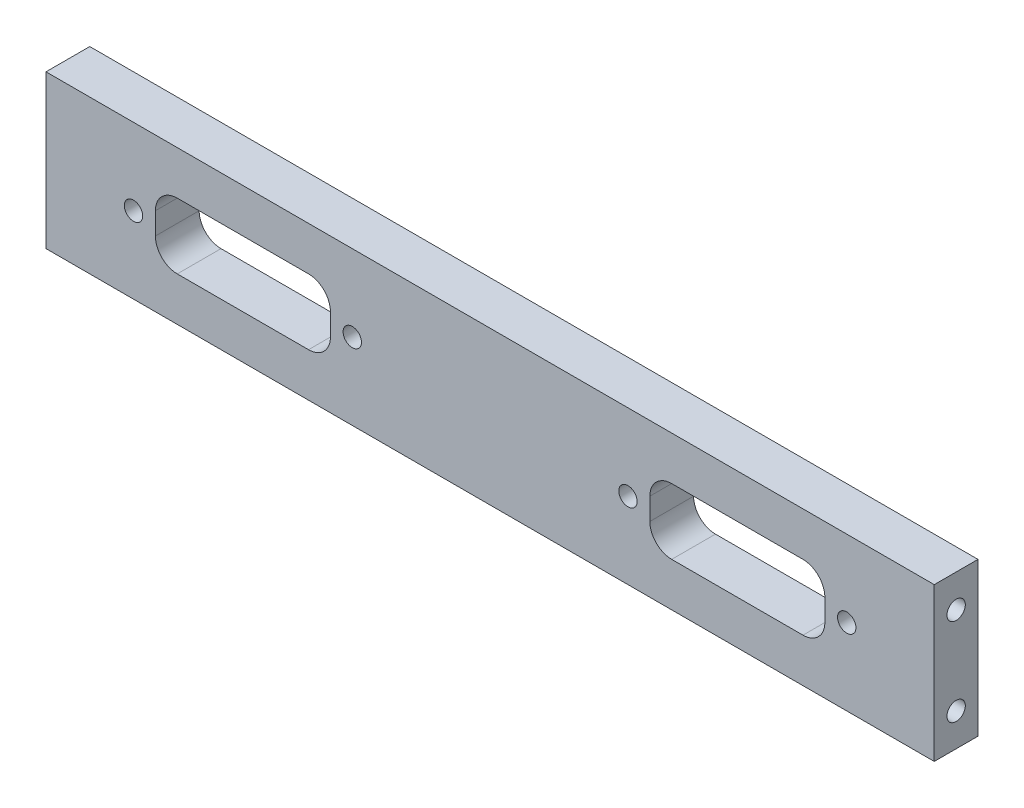
SolidWorks part; units mm, degrees
material "普通碳钢"
ref_plane "前视基准面" through (0, 0, 0) normal (0, 0, 1) x (1, 0, 0)
ref_plane "上视基准面" through (0, 0, 0) normal (0, 1, 0) x (1, 0, 0)
ref_plane "右视基准面" through (0, 0, 0) normal (1, 0, 0) x (0, 0, -1)
sketch "草图1" plane through (0, 0, 0) normal (0, 0, 1) x (1, 0, 0)
  line L1 (-101.5, -17.5) -> (101.5, -17.5)
  line L2 (-101.5, -17.5) -> (-101.5, 17.5)
  line L3 (-101.5, 17.5) -> (101.5, 17.5)
  line L4 (101.5, -17.5) -> (101.5, 17.5)
  line L5 (-101.5, -17.5) -> (101.5, 17.5) construction
  line L6 (-101.5, 17.5) -> (101.5, -17.5) construction
  point P0 (0, 0)
  dimension "D1" = 35
  dimension "D2" = 203
extrude "凸台-拉伸1" add sketch "草图1" along normal mid plane 10 contours L3 L4 L1 L2
hole_wizard "M5 螺纹孔1" positions "草图3" profile "草图2" tap size "M5" standard "GB"
sketch "草图3" plane through (-101.5, 0, 0) normal (-1, 0, 0) x (0, 0, 1)
  point P0 (0, 10)
  point P2 (0, -10)
  dimension "D1" = 20
  dimension "D2" = 10
sketch "草图2" plane through (-101.5, 10, 0) normal (0, 1, 0) x (0, 0, 1)
  line L0 (0, 0) -> (0, 15.2618)
  line L1 (0, 15.2618) -> (2.1, 14)
  line L2 (2.1, 14) -> (2.1, 0)
  line L5 (2.1, 0) -> (0, 0)
  line L10 (0, 15.2618) -> (-2.1, 14) construction
  line L11 (0, -6.35) -> (0, 107.95) construction
  dimension "螺纹孔钻头直径" = 4.2
  dimension "螺纹孔钻头深度" = 14
  dimension "导头角度" = 118
cosmetic thread "孔螺蚊线1" parameters "D1"=10, "D2"=5
cosmetic thread "孔螺蚊线2" parameters "D1"=10, "D2"=5
mirror "镜向1" about plane through (0, 0, 0) normal (1, 0, 0) of "M5 螺纹孔1"
sketch "草图4" plane through (0, 0, -5) normal (0, 0, -1) x (-1, 0, 0)
  line L0 (101.5, -17.5) -> (101.5, 17.5) construction
  line L1 (36.5, -7.5) -> (76.5, -7.5)
  line L2 (36.5, -7.5) -> (36.5, 7.5)
  line L3 (36.5, 7.5) -> (76.5, 7.5)
  line L4 (76.5, -7.5) -> (76.5, 7.5)
  line L5 (36.5, -7.5) -> (76.5, 7.5) construction
  line L6 (36.5, 7.5) -> (76.5, -7.5) construction
  point P0 (56.5, 0)
  dimension "D1" = 40
  dimension "D2" = 15
  dimension "D3" = 25
extrude "切除-拉伸1" cut sketch "草图4" against normal blind 10
fillet "圆角1" radius 5 4 edges at (-76.5, -7.5, 0) (-76.5, 7.5, 0) (-36.5, -7.5, 0) (-36.5, 7.5, 0)
hole_wizard "Ø4.2 (4.2) 直径孔1" positions "草图6" profile "草图5" hole size "Ø4.2" standard "GB" end condition through all
sketch "草图6" plane through (0, 0, -5) normal (0, 0, -1) x (-1, 0, 0)
  line L0 (101.5, -17.5) -> (101.5, 17.5) construction
  point P0 (81.5, 0)
  point P2 (31.5, 0)
  dimension "D1" = 20
  dimension "D2" = 50
sketch "草图5" plane through (-81.5, 0, -5) normal (1, 0, 0) x (0, 1, 0)
  line L0 (0, 0) -> (0, 10)
  line L1 (0, 10) -> (2.1, 10)
  line L2 (2.1, 10) -> (2.1, 0)
  line L5 (2.1, 0) -> (0, 0)
  line L11 (0, -6.35) -> (0, 107.95) construction
  dimension "通孔孔直径" = 4.2
  dimension "通孔孔深度" = 10
mirror "镜向2" about plane through (0, 0, 0) normal (1, 0, 0) of "Ø4.2 (4.2) 直径孔1", "切除-拉伸1", "圆角1"
